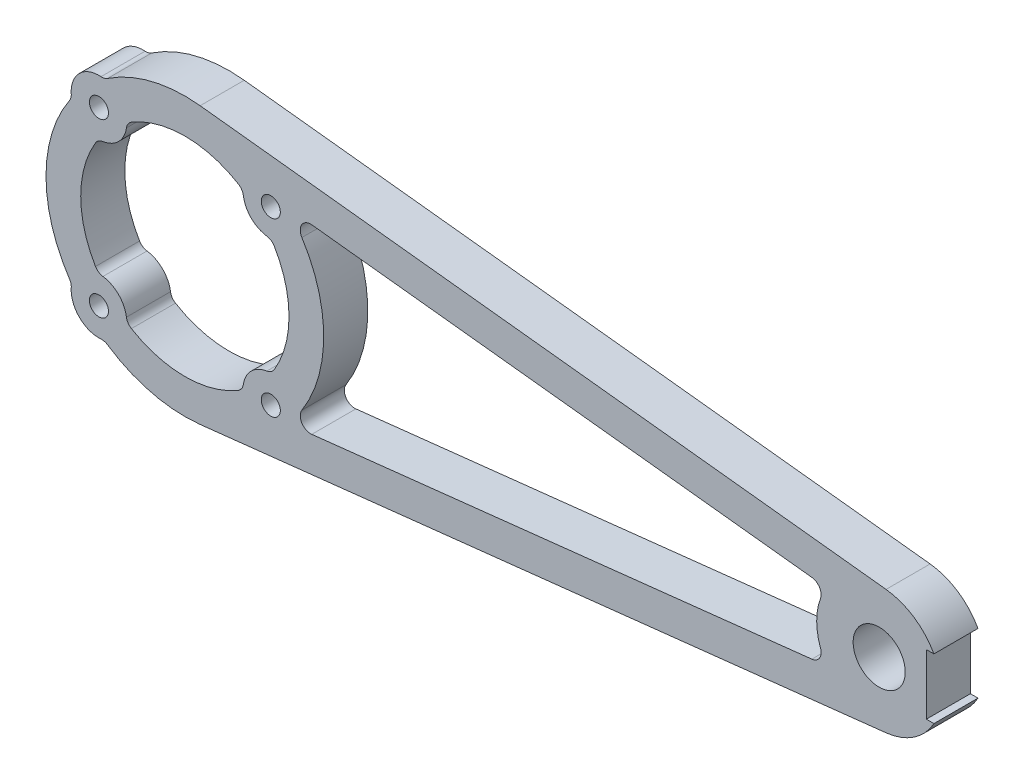
SolidWorks part; units mm, degrees
ref_plane "Front Plane" through (0, 0, 0) normal (0, 0, 1) x (1, 0, 0)
ref_plane "Top Plane" through (0, 0, 0) normal (0, 1, 0) x (1, 0, 0)
ref_plane "Right Plane" through (0, 0, 0) normal (1, 0, 0) x (0, 0, -1)
ref_plane "Plane1" through (0, 0, 0) normal (0, 0, -1) x (-1, 0, 0)
sketch "Sketch1" plane through (0, 0, 0) normal (0, 0, -1) x (-1, 0, 0)
  line L0 (-18.2817, -13.0683) -> (-90.3038, -5.0975)
  line L1 (-90.3038, 5.0975) -> (-18.2817, 13.0683)
  line L2 (-106.7927, -4.343) -> (-107.8828, -4.343)
  line L3 (-100.99, -8.9454) -> (-2.2, -19.8786)
  line L4 (-2.2, 19.8786) -> (-100.99, 8.9454)
  line L5 (-107.8828, 4.343) -> (-106.7927, 4.343)
  line L6 (-106.7927, 4.343) -> (-106.7927, -4.343)
  circle A0 centre (-100, 0) radius 3.75
  circle A1 centre (12.3744, -12.3744) radius 1.375
  circle A2 centre (12.3744, 12.3744) radius 1.375
  circle A3 centre (-12.3744, 12.3744) radius 1.375
  circle A4 centre (-12.3744, -12.3744) radius 1.375
  arc A5 (-11.8001, -8.4158) -> (-12.8719, -7.7015) centre (-11.5848, -6.9313) cw
  arc A6 (-12.8719, -7.7015) -> (-12.8719, 7.7015) centre (0, 0) cw
  arc A7 (-12.8719, 7.7015) -> (-11.8001, 8.4158) centre (-11.5848, 6.9313) cw
  arc A8 (-11.8001, 8.4158) -> (-8.4158, 11.8001) centre (-12.3744, 12.3744) ccw
  arc A9 (-8.4158, 11.8001) -> (-7.7015, 12.8719) centre (-6.9313, 11.5848) cw
  arc A10 (-7.7015, 12.8719) -> (7.7015, 12.8719) centre (0, 0) cw
  arc A11 (7.7015, 12.8719) -> (8.4158, 11.8001) centre (6.9313, 11.5848) cw
  arc A12 (8.4158, 11.8001) -> (11.8001, 8.4158) centre (12.3744, 12.3744) ccw
  arc A13 (11.8001, 8.4158) -> (12.8719, 7.7015) centre (11.5848, 6.9313) cw
  arc A14 (12.8719, 7.7015) -> (12.8719, -7.7015) centre (0, 0) cw
  arc A15 (12.8719, -7.7015) -> (11.8001, -8.4158) centre (11.5848, -6.9313) cw
  arc A16 (11.8001, -8.4158) -> (8.4158, -11.8001) centre (12.3744, -12.3744) ccw
  arc A17 (8.4158, -11.8001) -> (7.7015, -12.8719) centre (6.9313, -11.5848) cw
  arc A18 (7.7015, -12.8719) -> (-7.7015, -12.8719) centre (0, 0) cw
  arc A19 (-7.7015, -12.8719) -> (-8.4158, -11.8001) centre (-6.9313, -11.5848) cw
  arc A20 (-8.4158, -11.8001) -> (-11.8001, -8.4158) centre (-12.3744, -12.3744) ccw
  arc A21 (-90.3038, -5.0975) -> (-91.5476, -3.0914) centre (-90.1388, -3.6066) cw
  arc A22 (-91.5476, -3.0914) -> (-91.5476, 3.0914) centre (-100, 0) ccw
  arc A23 (-91.5476, 3.0914) -> (-90.3038, 5.0975) centre (-90.1388, 3.6066) cw
  arc A24 (-18.2817, 13.0683) -> (-16.8527, 10.7697) centre (-18.1167, 11.5774) cw
  arc A25 (-16.8527, 10.7697) -> (-16.8527, -10.7697) centre (0, 0) ccw
  arc A26 (-16.8527, -10.7697) -> (-18.2817, -13.0683) centre (-18.1167, -11.5774) cw
  arc A27 (-107.8828, -4.343) -> (-100.99, -8.9454) centre (-100, 0) ccw
  arc A28 (-2.2, -19.8786) -> (11.1352, -16.6135) centre (0, 0) ccw
  arc A29 (11.1352, -16.6135) -> (12.0805, -16.3636) centre (11.9703, -17.8595) cw
  arc A30 (12.0805, -16.3636) -> (16.3636, -12.0805) centre (12.3744, -12.3744) ccw
  arc A31 (16.3636, -12.0805) -> (16.6135, -11.1352) centre (17.8595, -11.9703) cw
  arc A32 (16.6135, -11.1352) -> (16.6135, 11.1352) centre (0, 0) ccw
  arc A33 (16.6135, 11.1352) -> (16.3636, 12.0805) centre (17.8595, 11.9703) cw
  arc A34 (16.3636, 12.0805) -> (12.0805, 16.3636) centre (12.3744, 12.3744) ccw
  arc A35 (12.0805, 16.3636) -> (11.1352, 16.6135) centre (11.9703, 17.8595) cw
  arc A36 (11.1352, 16.6135) -> (-2.2, 19.8786) centre (0, 0) ccw
  arc A37 (-100.99, 8.9454) -> (-107.8828, 4.343) centre (-100, 0) ccw
extrude "Boss-Extrude1" add sketch "Sketch1" against normal blind 6.35
